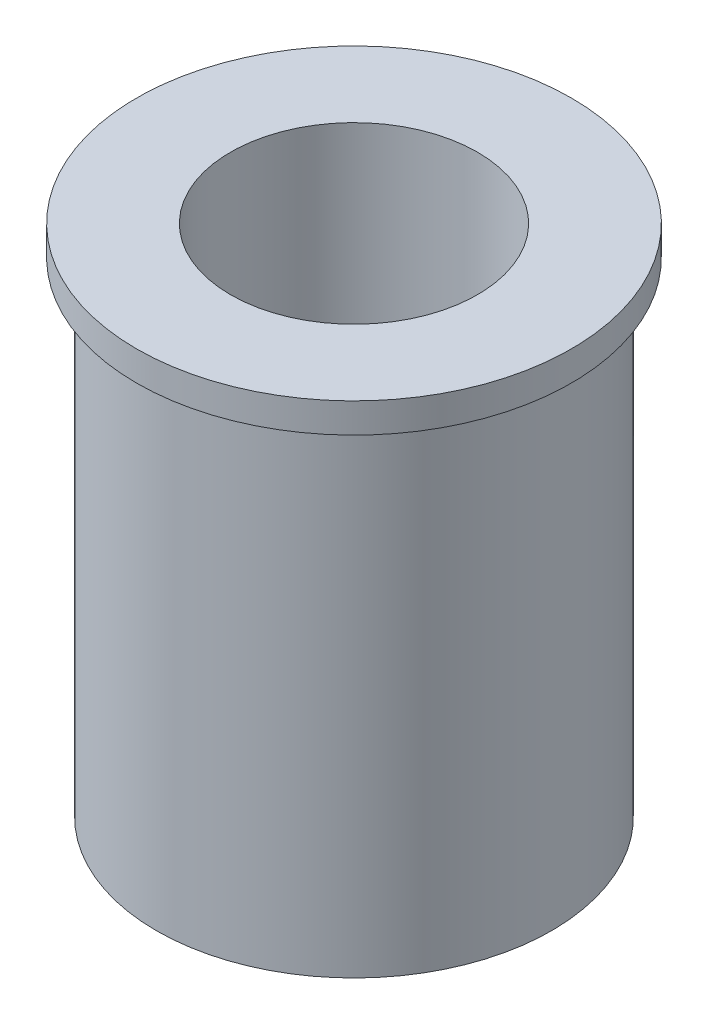
SolidWorks part; units mm, degrees
material "Messing"
ref_plane "Ebene vorne" through (0, 0, 0) normal (0, 0, 1) x (1, 0, 0)
ref_plane "Ebene oben" through (0, 0, 0) normal (0, 1, 0) x (1, 0, 0)
ref_plane "Ebene rechts" through (0, 0, 0) normal (1, 0, 0) x (0, 0, -1)
sketch "Skizze1" plane through (0, 0, 0) normal (0, 1, 0) x (1, 0, 0)
  circle A0 centre (0, 0) radius 2
  circle A1 centre (0, 0) radius 1.25
  dimension "D1" = 2.5
  dimension "D2" = 4
extrude "Aufsatz-Linear austragen1" add sketch "Skizze1" along normal blind 4.9
sketch "Skizze2" plane through (0, 4.9, 0) normal (0, 1, 0) x (1, 0, 0)
  circle A0 centre (0, 0) radius 1.25
  circle A1 centre (0, 0) radius 2.2
  dimension "D1" = 4.4
extrude "Aufsatz-Linear austragen2" add sketch "Skizze2" along normal blind 0.3
